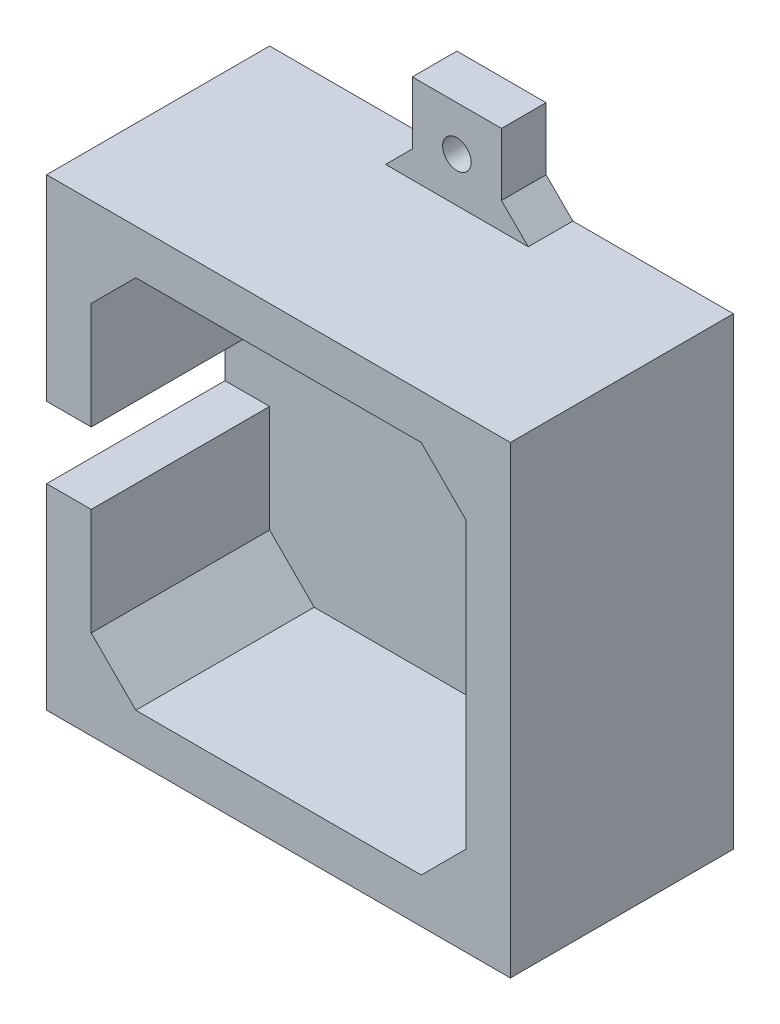
SolidWorks part; units mm, degrees
ref_plane "Ön Düzlem" through (0, 0, 0) normal (0, 0, 1) x (1, 0, 0)
ref_plane "Üst Düzlem" through (0, 0, 0) normal (0, 1, 0) x (1, 0, 0)
ref_plane "Sağ Düzlem" through (0, 0, 0) normal (1, 0, 0) x (0, 0, -1)
sketch "Çizim1" plane through (0, 0, 0) normal (0, 0, 1) x (1, 0, 0)
  line L0 (-5, 48.1705) -> (47, 48.1705)
  line L1 (5, 1.1705) -> (37, 1.1705)
  line L2 (0, 6.1705) -> (0, 38.1705)
  line L3 (5, 43.1705) -> (37, 43.1705)
  line L4 (42, 6.1705) -> (42, 38.1705)
  line L5 (47, 48.1705) -> (47, -3.8295)
  line L6 (47, -3.8295) -> (-5, -3.8295)
  line L7 (-5, 48.1705) -> (-5, -3.8295)
  line L8 (37, 43.1705) -> (42, 38.1705)
  line L9 (0, 38.1705) -> (5, 43.1705)
  line L10 (0, 6.1705) -> (5, 1.1705)
  line L11 (37, 1.1705) -> (42, 6.1705)
  point P0 (0, 1.1705)
  point P1 (42, 43.1705)
  point P2 (0, 43.1705)
  point P3 (42, 1.1705)
  dimension "D1" = 42
  dimension "D2" = 42
  dimension "D3" = 5
  dimension "D4" = 5
  dimension "D5" = 5
  dimension "D6" = 5
extrude "Yükseklik-Ekstrüzyon4" add sketch "Çizim1" along normal blind 20
sketch "Çizim3" plane through (47, 0, 0) normal (1, 0, 0) x (0, 0, -1)
  line L1 (0, 48.1705) -> (5, 48.1705)
  line L2 (0, 48.1705) -> (0, -3.8295)
  line L3 (0, -3.8295) -> (5, -3.8295)
  line L4 (5, 48.1705) -> (5, -3.8295)
  dimension "D1" = 52
  dimension "D2" = 5
extrude "Yükseklik-Ekstrüzyon5" add sketch "Çizim3" against normal blind 52
sketch "Çizim5" plane through (-5, 0, 0) normal (-1, 0, 0) x (0, 0, 1)
  line L0 (-5, 22.1705) -> (0, 22.1705)
  line L1 (0, 22.1705) -> (0, 26.1705)
  line L2 (0, 26.1705) -> (8, 26.1705)
  line L3 (8, 26.1705) -> (8, 18.1705)
  line L4 (8, 18.1705) -> (0, 18.1705)
  line L5 (0, 18.1705) -> (0, 22.1705)
  dimension "D1" = 5
  dimension "D2" = 4
  dimension "D3" = 8
  dimension "D4" = 8
  dimension "D5" = 8
extrude "Kes-Ekstrüzyon2" cut sketch "Çizim5" against normal blind 33 contours L5 L4 L3 L2 L1
sketch "Çizim6" plane through (0, 0, -5) normal (0, 0, -1) x (-1, 0, 0)
  line L0 (-26, 58.1705) -> (-21, 58.1705)
  line L1 (-21, 58.1705) -> (-16, 58.1705)
  line L2 (-16, 58.1705) -> (-16, 48.1705)
  line L3 (-16, 48.1705) -> (-26, 48.1705)
  line L4 (-26, 48.1705) -> (-26, 58.1705)
  line L5 (-26, -3.8295) -> (-26, -13.8295)
  line L6 (-26, -13.8295) -> (-16, -13.8295)
  line L7 (-16, -13.8295) -> (-16, -3.8295)
  line L8 (-16, -3.8295) -> (-26, -3.8295)
  circle A0 centre (-21, 53.1705) radius 1.6
  circle A1 centre (-21, -8.8295) radius 1.6
  dimension "D8" = 3.2
  dimension "D9" = 3.2
  dimension "D1" = 10
  dimension "D2" = 5
  dimension "D3" = 10
  dimension "D4" = 10
  dimension "D5" = 10
  dimension "D6" = 10
  dimension "D7" = 10
extrude "Yükseklik-Ekstrüzyon6" add sketch "Çizim6" against normal blind 5
chamfer "Pah3" distance 3 angle 45 4 edges at (16, -3.8295, -2.5) (26, -3.8295, -2.5) (26, 48.1705, -2.5) (16, 48.1705, -2.5)
sketch "Çizim7" plane through (-5, 0, 0) normal (-1, 0, 0) x (0, 0, 1)
  line L1 (8, 26.1705) -> (23.2099, 26.1705)
  line L2 (8, 26.1705) -> (8, 18.1705)
  line L3 (8, 18.1705) -> (23.2099, 18.1705)
  line L4 (23.2099, 26.1705) -> (23.2099, 18.1705)
extrude "Kes-Ekstrüzyon3" cut sketch "Çizim7" against normal blind 16
